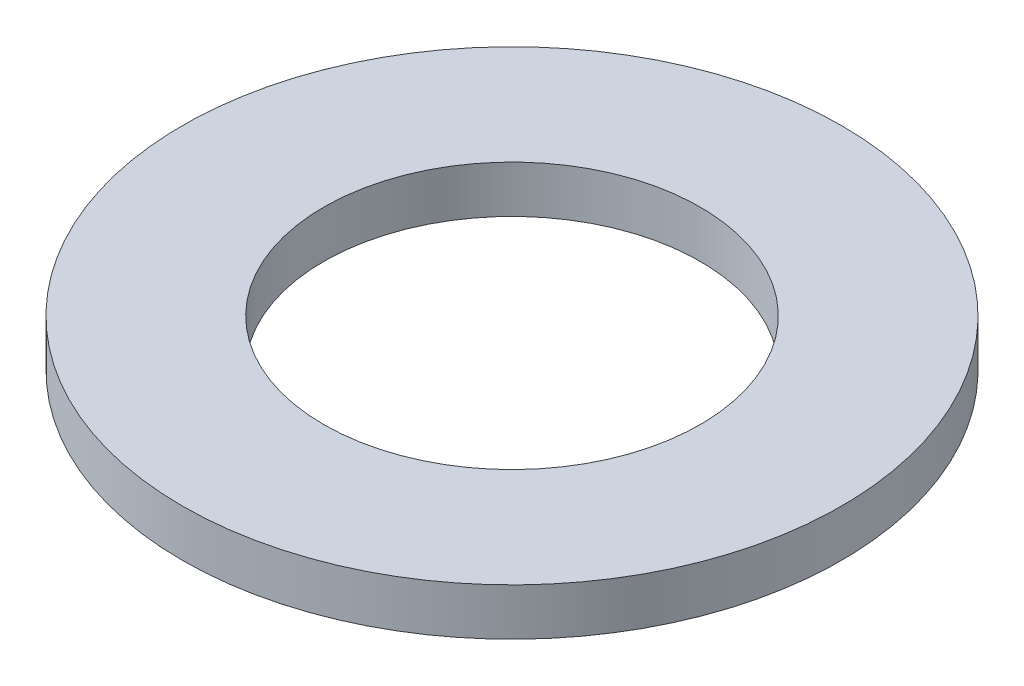
SolidWorks part; units mm, degrees
material "Alloy Steel (SS)"
ref_plane "Front Plane" through (0, 0, 0) normal (0, 0, 1) x (1, 0, 0)
ref_plane "Top Plane" through (0, 0, 0) normal (0, 1, 0) x (1, 0, 0)
ref_plane "Right Plane" through (0, 0, 0) normal (1, 0, 0) x (0, 0, -1)
sketch "Sketch1" plane through (0, 0, 0) normal (0, 1, 0) x (1, 0, 0)
  circle A0 centre (0, 0) radius 11.1125
  circle A1 centre (0, 0) radius 6.35
  dimension "D1" = 12.7
  dimension "D2" = 22.225
extrude "Boss-Extrude1" add sketch "Sketch1" along normal blind 1.5875
